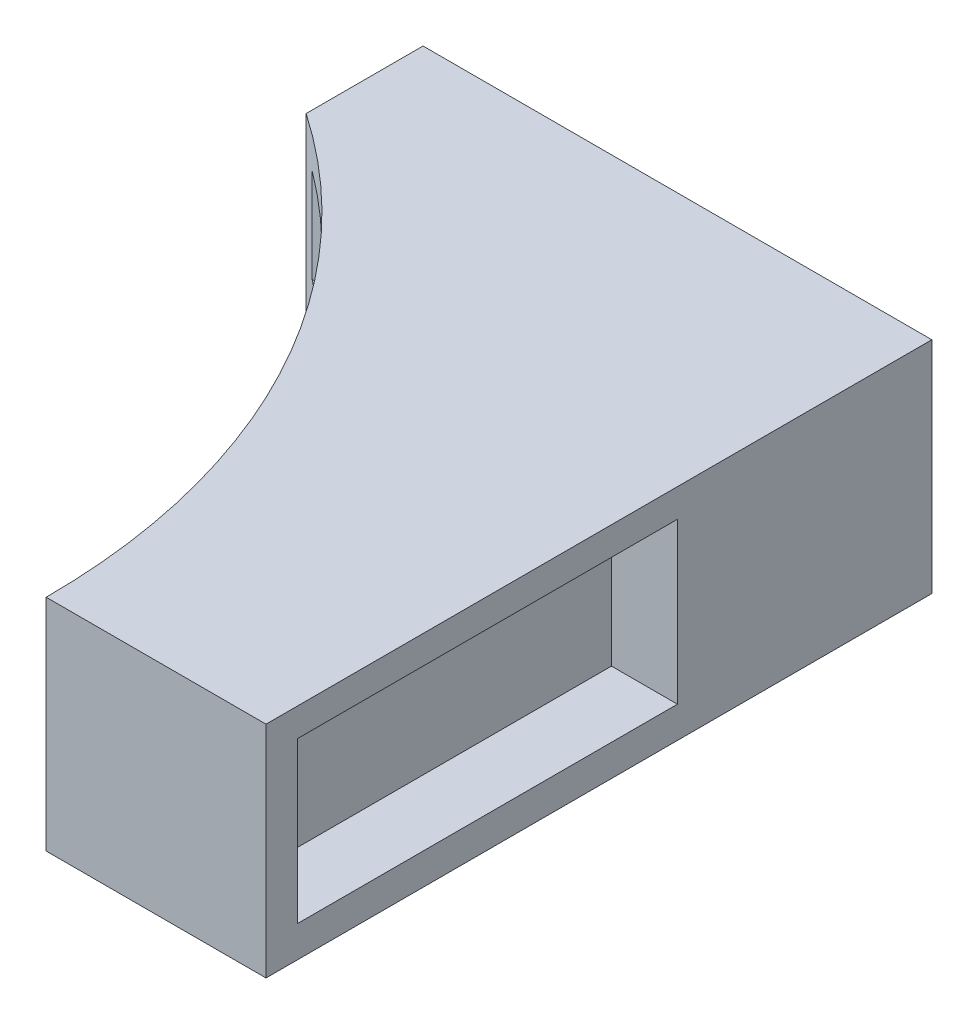
SolidWorks part; units mm, degrees
ref_plane "Front Plane" through (0, 0, 0) normal (0, 0, 1) x (1, 0, 0)
ref_plane "Top Plane" through (0, 0, 0) normal (0, 1, 0) x (1, 0, 0)
ref_plane "Right Plane" through (0, 0, 0) normal (1, 0, 0) x (0, 0, -1)
other "Configuration Table"
sketch "Sketch1" plane through (0, 0, 0) normal (0, 1, 0) x (1, 0, 0)
  line L1 (7, 21.2) -> (-21.2, 21.2)
  line L2 (0, 0) -> (7, 0)
  line L3 (7, 0) -> (7, 21.2)
  arc A0 (-21.2, 21.2) -> (0, 0) centre (-21.2, 0) cw
  dimension "D1" = 21.2
  dimension "D2" = 7
  dimension "D3" = 21.2
extrude "Boss-Extrude1" add sketch "Sketch1" along normal blind 7
sketch "Sketch2" plane through (0, 7, 0) normal (0, 1, 0) x (1, 0, 0)
  line L0 (-9.2, 17.4768) -> (-9.2, 21.2)
  line L1 (7, 21.2) -> (-21.2, 21.2) construction
  line L2 (-9.2, 21.2) -> (-21.2, 21.2)
  arc A0 (0, 0) -> (-21.2, 21.2) centre (-21.2, 0) ccw construction
  arc A1 (-21.2, 21.2) -> (-9.2, 17.4768) centre (-21.2, 0) cw
  dimension "D1" = 12
extrude "Cut-Extrude1" cut sketch "Sketch2" against normal through all
sketch "Sketch5" plane through (0, 0, 0) normal (1, 0, 0) x (0, 0, -1)
  line L1 (17, 6) -> (2, 6)
  line L2 (17, 6) -> (17, 3)
  line L3 (17, 3) -> (2, 3)
  line L4 (2, 6) -> (2, 3)
  line L5 (17.4768, 7) -> (0, 7) construction
  line L6 (0, 7) -> (0, 0) construction
  dimension "D1" = 15
  dimension "D2" = 3
  dimension "D3" = 1
  dimension "D4" = 2
extrude "Cut-Extrude3" cut sketch "Sketch5" against normal blind 10
sketch "Sketch6" plane through (7, 0, 0) normal (1, 0, 0) x (0, 0, -1)
  line L0 (0, 7) -> (0, 0) construction
  line L1 (1, 1) -> (13.1, 1)
  line L2 (1, 1) -> (1, 6.1)
  line L3 (1, 6.1) -> (13.1, 6.1)
  line L4 (13.1, 1) -> (13.1, 6.1)
  line L5 (0, 0) -> (21.2, 0) construction
  dimension "D1" = 1
  dimension "D2" = 12.1
  dimension "D3" = 5.1
  dimension "D4" = 1
extrude "Cut-Extrude4" cut sketch "Sketch6" against normal blind 2.1
